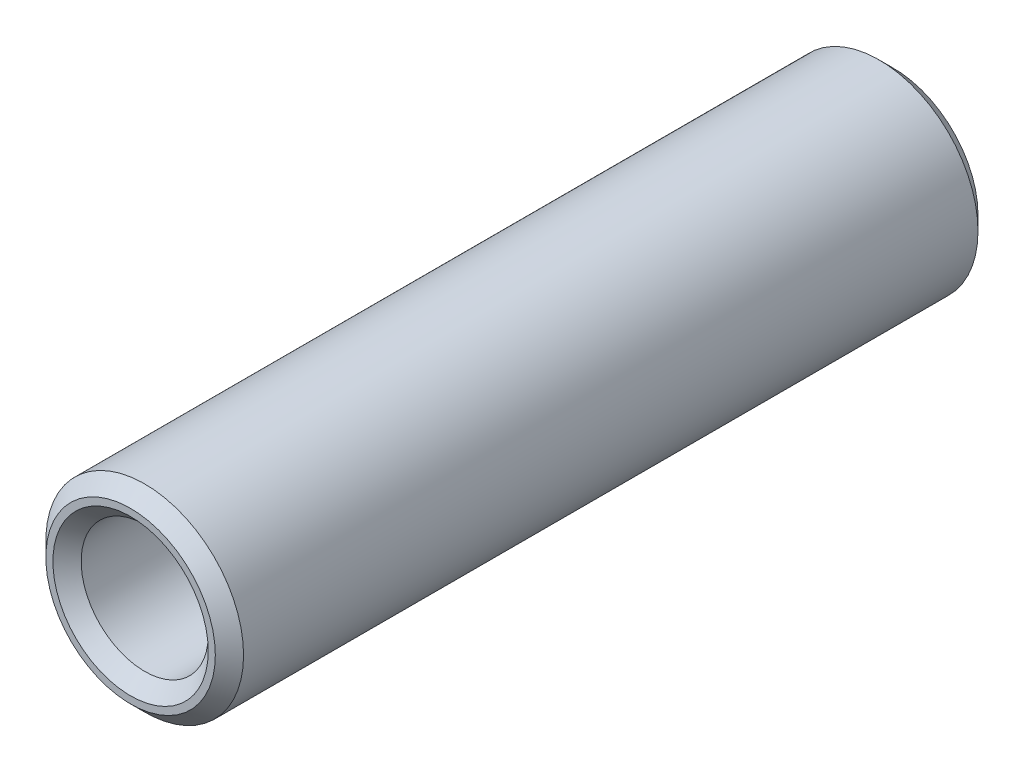
SolidWorks part; units mm, degrees
ref_plane "Plan de face" through (0, 0, 0) normal (0, 0, 1) x (1, 0, 0)
ref_plane "Plan de dessus" through (0, 0, 0) normal (0, 1, 0) x (1, 0, 0)
ref_plane "Plan de droite" through (0, 0, 0) normal (1, 0, 0) x (0, 0, -1)
sketch "Esquisse1" plane through (0, 0, 0) normal (0, 0, 1) x (1, 0, 0)
  circle A0 centre (0, 0) radius 2.25
  circle A1 centre (0, 0) radius 3.5
  dimension "D1" = 4.5
  dimension "D2" = 7
extrude "Boss.-Extru.1" add sketch "Esquisse1" along normal blind 27
sketch "Esquisse2" plane through (0, 0, 27) normal (0, 0, 1) x (1, 0, 0)
sketch "Esquisse3" plane through (0, 0, 27) normal (0, 0, 1) x (1, 0, 0)
chamfer "Chanfrein2" distance 0.5 angle 45 2 edges at (2.25, 0, 0) (3.5, 0, 0)
chamfer "Chanfrein3" distance 0.5 angle 45 2 edges at (2.25, 0, 27) (3.5, 0, 27)
sketch3d "Esquisse3D1"
  circle A0 centre (0, -12.3445, 0) radius 6
  circle A1 centre (0, -12.3445, 0) radius 4.5
  point P2 (0, -12.3445, 6)
  point P4 (0, -12.3445, 4.5)
  dimension "D1" = 12
  dimension "D2" = 9
